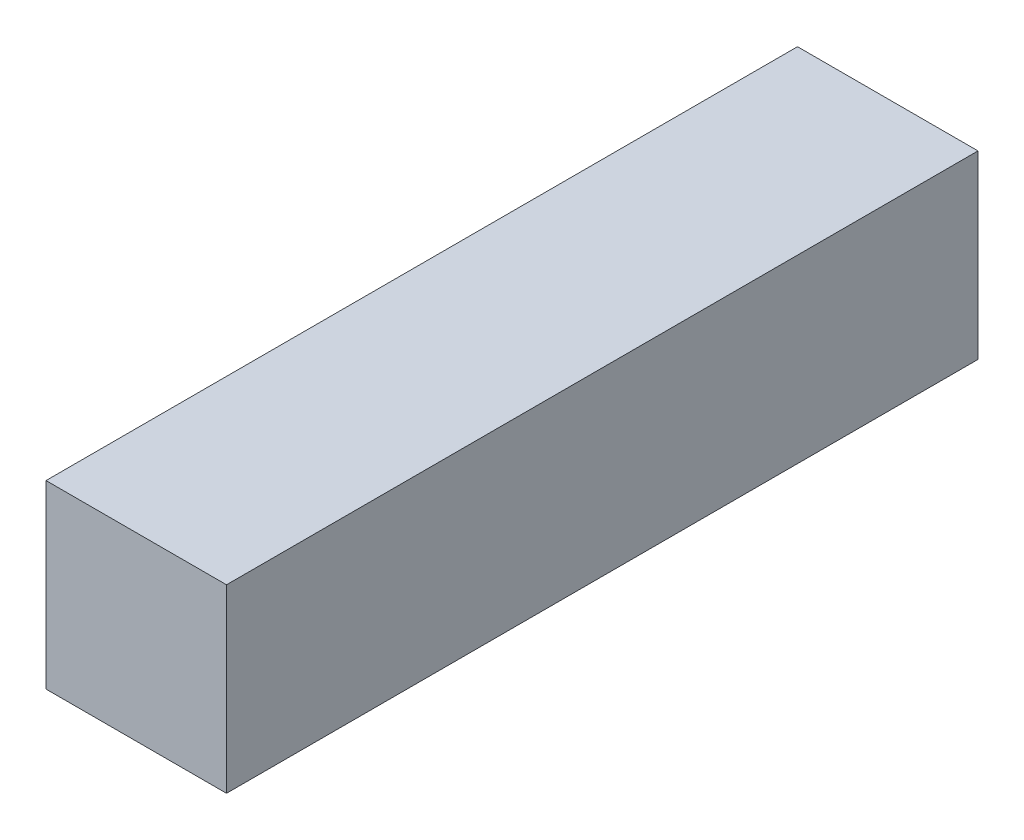
SolidWorks part; units mm, degrees
ref_plane "Piano frontale" through (0, 0, 0) normal (0, 0, 1) x (1, 0, 0)
ref_plane "Piano superiore" through (0, 0, 0) normal (0, 1, 0) x (1, 0, 0)
ref_plane "Piano destro" through (0, 0, 0) normal (1, 0, 0) x (0, 0, -1)
sketch "Sketch1" plane through (0, 0, 0) normal (0, 0, 1) x (1, 0, 0)
  line L1 (0, 0) -> (4.7625, 0)
  line L2 (0, 0) -> (0, 4.765)
  line L3 (0, 4.765) -> (4.7625, 4.765)
  line L4 (4.7625, 0) -> (4.7625, 4.765)
  dimension "D1" = 4.7625
  dimension "D2" = 4.765
extrude "Boss-Extrude1" add sketch "Sketch1" along normal blind 19.8272
